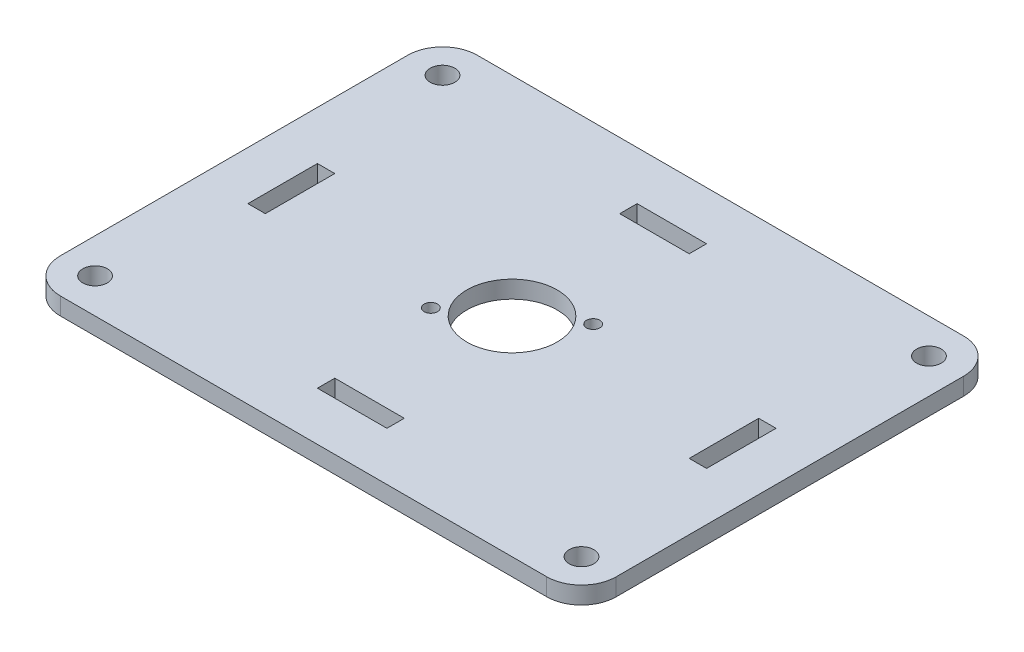
SolidWorks part; units mm, degrees
material "Acrylic (Medium-high impact)"
ref_plane "Front Plane" through (0, 0, 0) normal (0, 0, 1) x (1, 0, 0)
ref_plane "Top Plane" through (0, 0, 0) normal (0, 1, 0) x (1, 0, 0)
ref_plane "Right Plane" through (0, 0, 0) normal (1, 0, 0) x (0, 0, -1)
sketch "Sketch1" plane through (0, 0, 0) normal (0, 1, 0) x (1, 0, 0)
  line L1 (-50.8, -38.1) -> (50.8, -38.1)
  line L2 (-50.8, -38.1) -> (-50.8, 38.1)
  line L3 (-50.8, 38.1) -> (50.8, 38.1)
  line L4 (50.8, -38.1) -> (50.8, 38.1)
  line L5 (-50.8, -38.1) -> (50.8, 38.1) construction
  line L6 (-50.8, 38.1) -> (50.8, -38.1) construction
  point P0 (0, 0)
  dimension "D1" = 101.6
  dimension "D2" = 76.2
extrude "Boss-Extrude1" add sketch "Sketch1" along normal blind 3.175
fillet "Fillet1" radius 6.35 4 edges at (50.8, 1.5875, 38.1) (50.8, 1.5875, -38.1) (-50.8, 1.5875, -38.1) (-50.8, 1.5875, 38.1)
sketch "Sketch2" plane through (0, 3.175, 0) normal (0, 1, 0) x (1, 0, 0)
  line L0 (-50.8, 0) -> (-41.91, 0) construction
  line L1 (-50.8, 31.75) -> (-50.8, -31.75) construction
  line L2 (0, 38.1) -> (0, 29.21) construction
  line L3 (44.45, 38.1) -> (-44.45, 38.1) construction
  line L4 (50.8, 0) -> (41.91, 0) construction
  line L5 (50.8, -31.75) -> (50.8, 31.75) construction
  line L6 (0, -38.1) -> (0, -29.21) construction
  line L7 (-44.45, -38.1) -> (44.45, -38.1) construction
  line L8 (-41.91, 0) -> (-41.91, 6.35)
  line L9 (-41.91, 6.35) -> (-38.735, 6.35)
  line L10 (-38.735, 6.35) -> (-38.735, -6.35)
  line L11 (-38.735, -6.35) -> (-41.91, -6.35)
  line L12 (-41.91, -6.35) -> (-41.91, 0)
  line L13 (0, 29.21) -> (6.35, 29.21)
  line L14 (6.35, 29.21) -> (6.35, 26.035)
  line L15 (6.35, 26.035) -> (-6.35, 26.035)
  line L16 (-6.35, 26.035) -> (-6.35, 29.21)
  line L17 (-6.35, 29.21) -> (0, 29.21)
  line L18 (41.91, 0) -> (41.91, 6.35)
  line L19 (41.91, 6.35) -> (38.735, 6.35)
  line L20 (38.735, 6.35) -> (38.735, -6.35)
  line L21 (38.735, -6.35) -> (41.91, -6.35)
  line L22 (41.91, -6.35) -> (41.91, 0)
  line L23 (0, -29.21) -> (6.35, -29.21)
  line L24 (6.35, -29.21) -> (6.35, -26.035)
  line L25 (6.35, -26.035) -> (-6.35, -26.035)
  line L26 (-6.35, -26.035) -> (-6.35, -29.21)
  line L27 (-6.35, -29.21) -> (0, -29.21)
  circle A0 centre (-44.45, 31.75) radius 2.2479
  circle A1 centre (44.45, 31.75) radius 2.2479
  circle A2 centre (44.45, -31.75) radius 2.2479
  circle A3 centre (-44.45, -31.75) radius 2.2479
  dimension "D1" = 4.4958
  dimension "D2" = 8.89
  dimension "D3" = 3.175
  dimension "D4" = 8.89
  dimension "D5" = 3.175
  dimension "D6" = 12.7
  dimension "D7" = 12.7
extrude "Cut-Extrude1" cut sketch "Sketch2" against normal through all
sketch "Sketch3" plane through (0, 3.175, 0) normal (0, 1, 0) x (1, 0, 0)
  line L1 (8.6995, 6.1341) -> (-8.6995, 6.1341) construction
  line L2 (11.2141, 10.16) -> (-11.2141, 10.16) construction
  line L3 (11.2141, 10.16) -> (11.2141, -10.16) construction
  line L4 (11.2141, -10.16) -> (-11.2141, -10.16) construction
  line L5 (-11.2141, 10.16) -> (-11.2141, -10.16) construction
  line L6 (11.2141, 10.16) -> (-11.2141, -10.16) construction
  line L7 (11.2141, -10.16) -> (-11.2141, 10.16) construction
  line L8 (8.6995, 6.1341) -> (8.6995, -6.1341) construction
  line L9 (8.6995, -6.1341) -> (-8.6995, -6.1341) construction
  line L10 (-8.6995, 6.1341) -> (-8.6995, -6.1341) construction
  line L11 (8.6995, 6.1341) -> (-8.6995, -6.1341) construction
  line L12 (8.6995, -6.1341) -> (-8.6995, 6.1341) construction
  circle A0 centre (0, 0) radius 8.255
  circle A1 centre (-8.6995, -6.1341) radius 1.2192
  circle A2 centre (8.6995, 6.1341) radius 1.2192
  point P3 (0, 0)
  dimension "D3" = 16.51
  dimension "D6" = 2.4384
  dimension "D1" = 20.32
  dimension "D2" = 22.4282
  dimension "D4" = 17.399
  dimension "D5" = 12.2682
extrude "Cut-Extrude2" cut sketch "Sketch3" against normal through all
